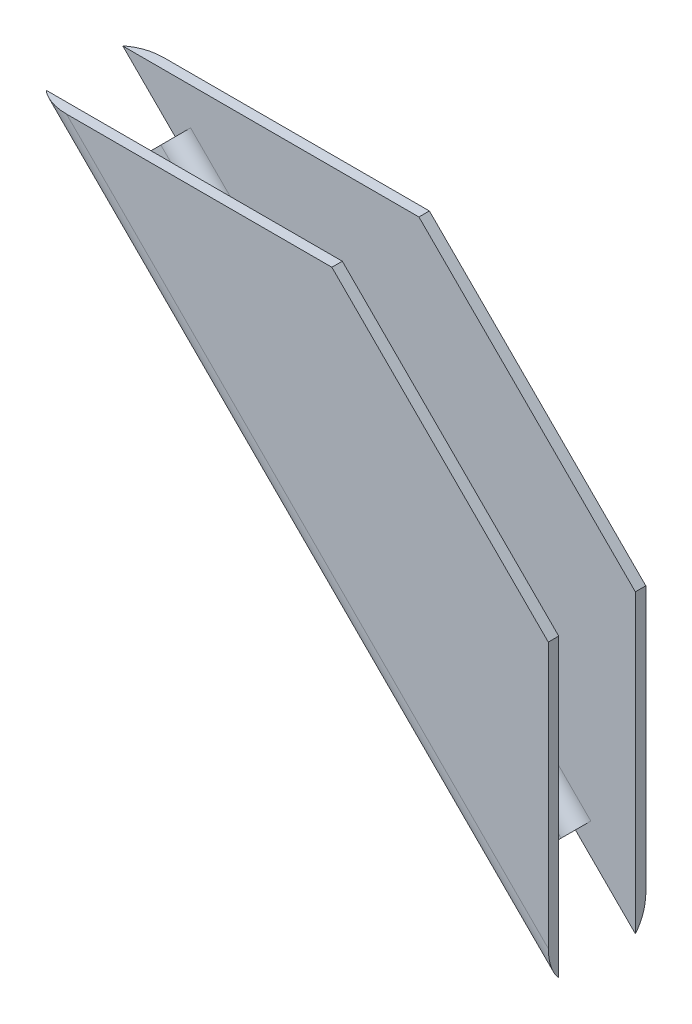
SolidWorks part; units mm, degrees
ref_plane "Front Plane" through (0, 0, 0) normal (0, 0, 1) x (1, 0, 0)
ref_plane "Top Plane" through (0, 0, 0) normal (0, 1, 0) x (1, 0, 0)
ref_plane "Right Plane" through (0, 0, 0) normal (1, 0, 0) x (0, 0, -1)
sketch "Sketch4" plane through (0, 0, 0) normal (0, 0, 1) x (1, 0, 0)
  line L0 (86.7673, 78.2228) -> (131.2173, 78.2228)
  line L1 (131.2173, 78.2228) -> (162.7848, 46.6553)
  line L2 (162.7848, 46.6553) -> (162.7848, 2.2053)
  line L3 (162.7848, 2.2053) -> (86.7673, 78.2228)
  line L4 (74.0598, 71.8728) -> (111.0598, 71.8728) construction
  line L5 (156.4348, 100.479) -> (156.4348, -16.996) construction
  dimension "D1" = 6.35
  dimension "D2" = 6.35
  dimension "D3" = 12.7075
  dimension "D4" = 135
  dimension "D5" = 44.45
extrude "Boss-Extrude1" add sketch "Sketch4" along normal mid plane 1.524 from offset 6.35
sketch "Sketch5" plane through (0, 0, 5.588) normal (0, 0, -1) x (-1, 0, 0)
  line L0 (-153.4115, 11.5786) -> (-95.0398, 69.9503)
  line L1 (-86.7673, 78.2228) -> (-162.7848, 2.2053) construction
  line L2 (-154.4891, 12.6563) -> (-96.1174, 71.0279)
  line L3 (-96.1174, 71.0279) -> (-95.0398, 69.9503)
  line L4 (-153.4115, 11.5786) -> (-154.4891, 12.6563)
  point P5 (-124.2256, 40.7645)
  dimension "D1" = 1.524
  dimension "D2" = 82.55
extrude "Boss-Extrude2" add sketch "Sketch5" along normal blind 12.7
mirror "Mirror2" about plane through (0, 0, 0) normal (0, 0, 1) of "Boss-Extrude1"
fillet "Fillet1" radius 2.54 2 edges at (125.3033, 41.8421, 5.588) (125.3033, 41.8421, -5.588)
fillet "Fillet2" radius 4.064 2 edges at (124.7761, 40.214, 7.112) (124.7761, 40.214, -7.112)
